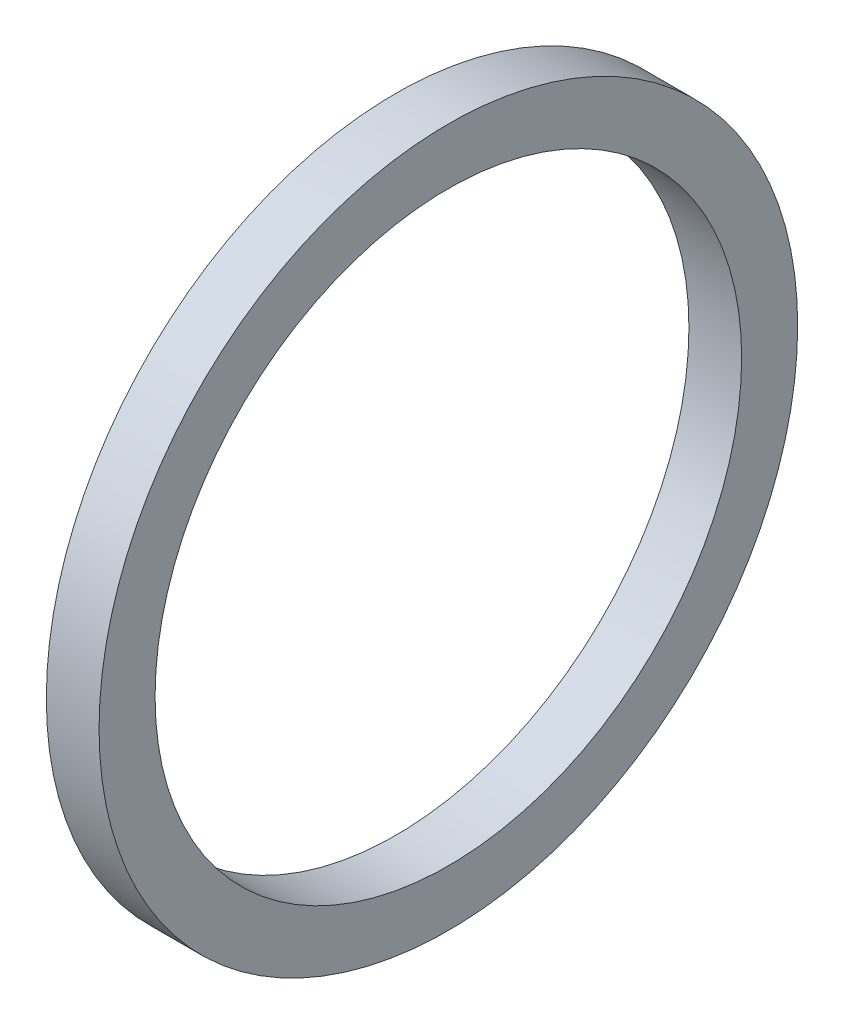
SolidWorks part; units mm, degrees
ref_plane "Front Plane" through (0, 0, 0) normal (0, 0, 1) x (1, 0, 0)
ref_plane "Top Plane" through (0, 0, 0) normal (0, 1, 0) x (1, 0, 0)
ref_plane "Right Plane" through (0, 0, 0) normal (1, 0, 0) x (0, 0, -1)
sketch "Sketch1" plane through (0, 0, 0) normal (0, 0, 1) x (1, 0, 0)
  line L0 (-43.7166, 0) -> (79.6876, 0) construction
  line L2 (0, -11.303) -> (2.032, -11.303)
  line L3 (0, -11.303) -> (0, -13.462)
  line L4 (0, -13.462) -> (2.032, -13.462)
  line L5 (2.032, -11.303) -> (2.032, -13.462)
  dimension "A" = 22.606
  dimension "B" = 26.924
  dimension "C" = 2.032
revolve "Revolve1" add sketch "Sketch1" angle 360 about L0
sketch "Sketch2" [suppressed] plane through (0, 0, 0) normal (0, 0, 1) x (1, 0, 0)
  line L0 (-34.685, 0) -> (47.6686, 0) construction
  circle A0 centre (2.54, -5.715) radius 0.762
  dimension "D1" = 2.54
  dimension "E" = 1.524
  dimension "D" = 18.034
revolve "Revolve3" [suppressed] add sketch "Sketch2" angle 360 about L0
